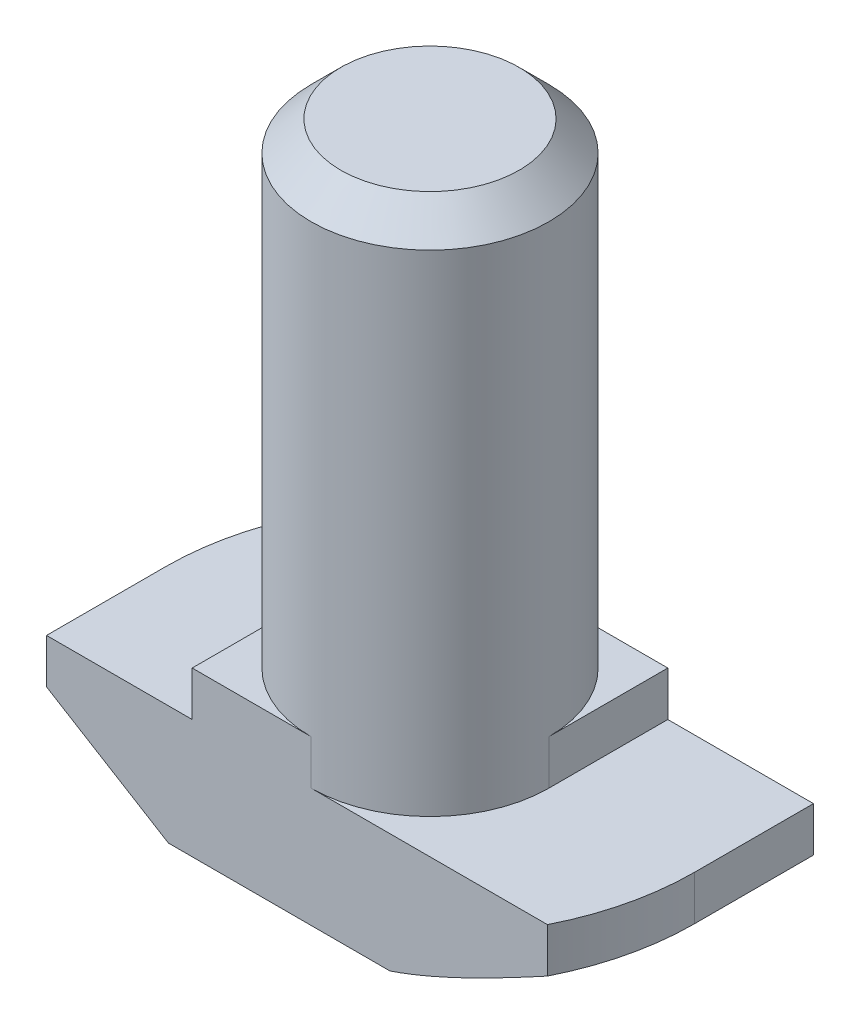
SolidWorks part; units mm, degrees
ref_plane "Спереди" through (0, 0, 0) normal (0, 0, 1) x (1, 0, 0)
ref_plane "Сверху" through (0, 0, 0) normal (0, 1, 0) x (1, 0, 0)
ref_plane "Справа" through (0, 0, 0) normal (1, 0, 0) x (0, 0, -1)
sketch "Эскиз1" plane through (0, 0, 0) normal (0, 0, 1) x (1, 0, 0)
  line L0 (8.9, 0) -> (-8.9, 0)
  line L1 (-8.9, 0) -> (-8.9, 4)
  line L2 (-8.9, 4) -> (-4, 4)
  line L3 (-4, 4) -> (-4, 5.5)
  line L4 (-4, 5.5) -> (4, 5.5)
  line L5 (0, 5.5) -> (0, 0) construction
  line L6 (4, 4) -> (4, 5.5)
  line L7 (8.9, 4) -> (4, 4)
  line L8 (8.9, 0) -> (8.9, 4)
  point P12 (-8.25, 2.6435)
  point P13 (-4, 3.6993)
  dimension "D1" = 8
  dimension "D2" = 17.8
  dimension "D3" = 5.5
  dimension "D4" = 1.5
extrude "Бобышка-Вытянуть1" add sketch "Эскиз1" along normal mid plane 8
sketch "Эскиз3" plane through (0, 5.5, 0) normal (0, 1, 0) x (1, 0, 0)
  line L1 (4, 4) -> (-4, 4) construction
  line L2 (-4, 0) -> (-4, 4)
  line L3 (-4, 4) -> (0, 4)
  line L4 (0, -4) -> (4, -4)
  line L5 (4, -4) -> (-4, -4) construction
  line L6 (4, -4) -> (4, 0)
  line L7 (4, -4) -> (4, 4) construction
  arc A0 (-4, 0) -> (0, 4) centre (0, 0) cw
  arc A1 (4, 0) -> (0, -4) centre (0, 0) cw
extrude "Вырез-Вытянуть1" cut sketch "Эскиз3" against normal up to surface (1.5 mm away) up to face at (-6.45, 4, 0)
sketch "Эскиз2" plane through (0, 5.5, 0) normal (0, 1, 0) x (1, 0, 0)
  circle A0 centre (0, 0) radius 4
  dimension "D1" = 8
extrude "Бобышка-Вытянуть2" add sketch "Эскиз2" along normal blind 16
cosmetic thread "Условное изображение резьбы1" parameters "D1"=16, "D2"=6.619
sketch "Эскиз4" plane through (0, 4, 0) normal (0, 1, 0) x (1, 0, 0)
  line L0 (-8.9, -4) -> (-8.9, 4) construction
  line L1 (8.9, -4) -> (8.9, 4) construction
  line L2 (-7.9505, 4) -> (-8.9, 4)
  line L3 (-8.9, 4) -> (-8.9, 0)
  line L4 (7.9505, -4) -> (8.9, -4)
  line L5 (8.9, -4) -> (8.9, 0)
  arc A0 (-8.9, 0) -> (-7.9505, 4) centre (0, 0) cw
  arc A1 (8.9, 0) -> (7.9505, -4) centre (0, 0) cw
extrude "Вырез-Вытянуть2" cut sketch "Эскиз4" against normal through all
sketch "Эскиз5" plane through (0, 0, 4) normal (0, 0, 1) x (1, 0, 0)
  line L0 (-8.9, 2.5) -> (-4.8, 0)
  line L1 (-8.9, 4) -> (-8.9, 0) construction
  line L2 (-8.9, 0) -> (7.9505, 0) construction
  line L3 (-4.8, 0) -> (-8.9, 0)
  line L4 (-8.9, 0) -> (-8.9, 2.5)
  line L6 (-4, 4) -> (-8.9, 4) construction
  line L7 (-4, 5.5) -> (-4, 4) construction
  point P6 (-4.9519, 0)
  point P9 (0, 0)
  point P10 (-4.6154, 0)
  point P12 (-8.25, 2.2665)
  point P15 (0, 0)
  dimension "D1" = 1.5
  dimension "D2" = 0.8
sketch "Эскиз6" plane through (0, 0, 0) normal (0, -1, 0) x (1, 0, 0)
  line L0 (0, -8.9) -> (8.9, -8.9)
  line L1 (8.9, -8.9) -> (8.9, 0)
  line L2 (0, 8.9) -> (-8.9, 8.9)
  line L3 (-8.9, 8.9) -> (-8.9, 0)
  arc A0 (-8.9, 0) -> (0, -8.9) centre (0, 0) ccw
  arc A1 (8.9, 0) -> (0, 8.9) centre (0, 0) ccw
  point P10 (0, 0)
sweep "Вырез-По траектории1" cut profiles "Эскиз5" path "Эскиз6"
chamfer "Фаска2" distance 1 angle 45 1 edges at (0, 21.5, 4)
